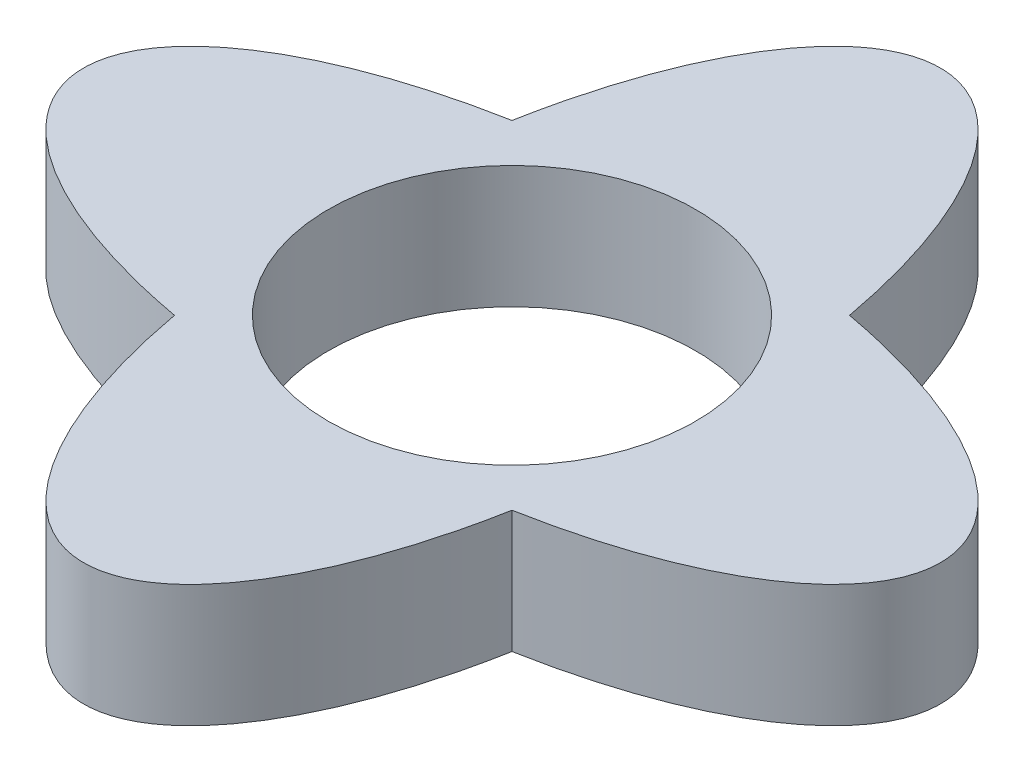
SolidWorks part; units mm, degrees
ref_plane "Front Plane" through (0, 0, 0) normal (0, 0, 1) x (1, 0, 0)
ref_plane "Top Plane" through (0, 0, 0) normal (0, 1, 0) x (1, 0, 0)
ref_plane "Right Plane" through (0, 0, 0) normal (1, 0, 0) x (0, 0, -1)
sketch "Sketch1" plane through (0, 0, 0) normal (0, 1, 0) x (1, 0, 0)
  circle A0 centre (0, 0) radius 3
  ellipse E0 centre (0, 0) end of major axis (0, 7) minor radius 3 (-2.7574, -2.7574) -> (2.7574, -2.7574) ccw
  ellipse E1 centre (0, 0) end of major axis (7, 0) minor radius 3 (-2.7574, 2.7574) -> (-2.7574, -2.7574) ccw
  ellipse E2 centre (0, 0) end of major axis (0, 7) minor radius 3 (2.7574, 2.7574) -> (-2.7574, 2.7574) ccw
  ellipse E3 centre (0, 0) end of major axis (7, 0) minor radius 3 (2.7574, -2.7574) -> (2.7574, 2.7574) ccw
  point P16 (0, 0)
extrude "Boss-Extrude1" add sketch "Sketch1" along normal blind 2
